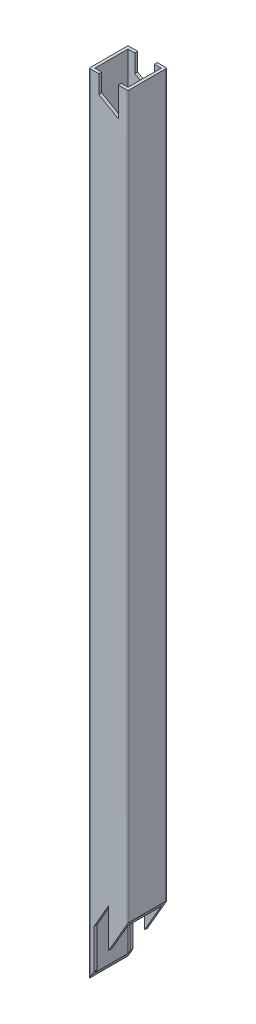
SolidWorks part; units mm, degrees
ref_plane "Front Plane" through (0, 0, 0) normal (0, 0, 1) x (1, 0, 0)
ref_plane "Top Plane" through (0, 0, 0) normal (0, 1, 0) x (1, 0, 0)
ref_plane "Right Plane" through (0, 0, 0) normal (1, 0, 0) x (0, 0, -1)
sketch "Sketch1" plane through (0, 0, 0) normal (0, 1, 0) x (1, 0, 0)
  line L0 (1.5, 1.5) -> (18.5, 1.5)
  line L1 (0.5, 0) -> (19.5, 0)
  line L2 (0, 0.5) -> (0, 19.5)
  line L3 (0.5, 20) -> (19.5, 20)
  line L4 (20, 0.5) -> (20, 19.5)
  line L5 (18.5, 1.5) -> (18.5, 18.5)
  line L6 (1.5, 18.5) -> (18.5, 18.5)
  line L7 (1.5, 1.5) -> (1.5, 18.5)
  arc A0 (19.5, 0) -> (20, 0.5) centre (19.5, 0.5) ccw
  arc A1 (0.5, 0) -> (0, 0.5) centre (0.5, 0.5) cw
  arc A2 (0, 19.5) -> (0.5, 20) centre (0.5, 19.5) cw
  arc A3 (19.5, 20) -> (20, 19.5) centre (19.5, 19.5) cw
  arc A4 (18.5, 1.5) -> (18.5, 1.5) centre (18.5, 1.5) ccw
  arc A5 (18.5, 18.5) -> (18.5, 18.5) centre (18.5, 18.5) cw
  arc A6 (1.5, 18.5) -> (1.5, 18.5) centre (1.5, 18.5) cw
  arc A7 (1.5, 1.5) -> (1.5, 1.5) centre (1.5, 1.5) cw
  point P9 (0, 0)
  dimension "D3" = 0.5
  dimension "D2" = 20
  dimension "20" = 20
  dimension "D4" = 1.5
extrude "Boss-Extrude1" add sketch "Sketch1" along normal blind 405
sketch "Sketch2" plane through (0, 0, 0) normal (0, 0, 1) x (1, 0, 0)
  line L1 (20, 405) -> (20, 0) construction
  line L4 (20, 0) -> (20, 34.641)
  line L5 (20, 34.641) -> (0, 0)
  line L6 (0, 0) -> (20, 0)
  dimension "D2" = 60
sketch "Sketch4" plane through (0, 0, -20) normal (0, 0, -1) x (-1, 0, 0)
  line L9 (-5, 405) -> (-5, 395.7735)
  line L10 (-19.5, 405) -> (-0.5, 405) construction
  line L12 (-15, 390) -> (-15, 405)
  line L15 (-5, 405) -> (-15, 405)
  line L16 (-15, 390) -> (-5, 395.7735)
  point P8 (-10, 405)
  point P10 (-10, 405)
  dimension "D1" = 15
  dimension "D2" = 10
  dimension "D3" = 60
extrude "Cut-Extrude2" cut sketch "Sketch4" against normal through all
extrude "Cut-Extrude4" cut sketch "Sketch2" against normal blind 20
sketch "Sketch6" plane through (0, 0, -20) normal (0, 0, -1) x (-1, 0, 0)
  line L0 (-2.59, 4.486) -> (-2.59, 24.486)
  line L1 (-19.5, 33.775) -> (-0.5, 0.866) construction
  line L2 (-2.59, 24.486) -> (-10.09, 37.4764)
  line L3 (-10.09, 37.4764) -> (-10.09, 17.4764)
  line L4 (-10.09, 17.4764) -> (-2.59, 4.486)
  dimension "D1" = 30
  dimension "D2" = 10
  dimension "D3" = 5.18
  dimension "D4" = 15
extrude "Cut-Extrude5" cut sketch "Sketch6" against normal through all
